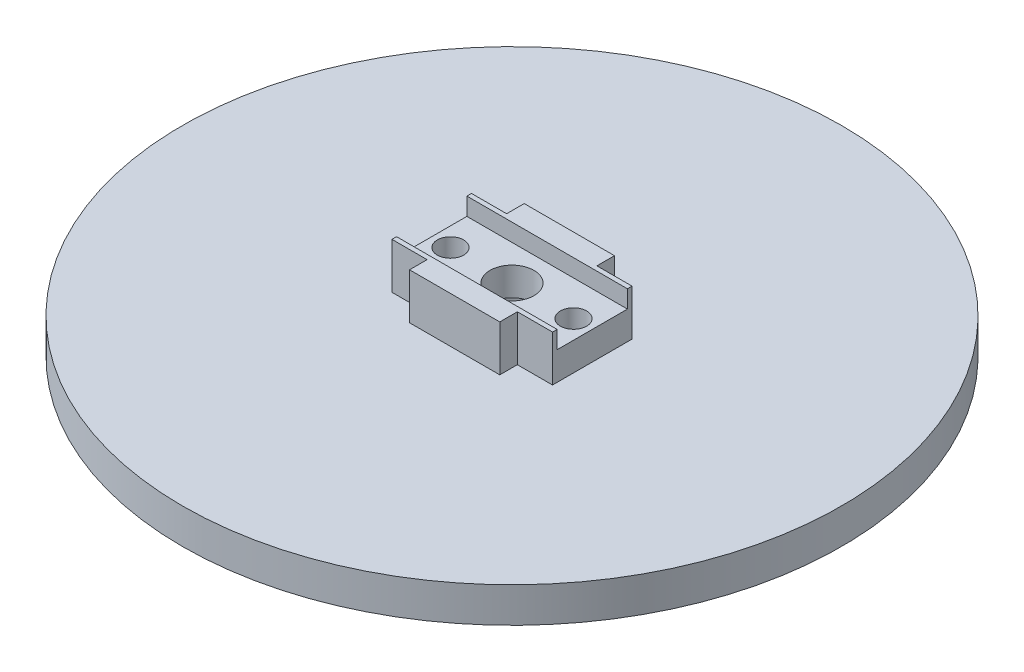
SolidWorks part; units mm, degrees
ref_plane "Front Plane" through (0, 0, 0) normal (0, 0, 1) x (1, 0, 0)
ref_plane "Top Plane" through (0, 0, 0) normal (0, 1, 0) x (1, 0, 0)
ref_plane "Right Plane" through (0, 0, 0) normal (1, 0, 0) x (0, 0, -1)
sketch "Sketch1" plane through (0, 0, 0) normal (0, 1, 0) x (1, 0, 0)
  circle A0 centre (0, 0) radius 37.5
  dimension "D1" = 75
extrude "Boss-Extrude1" add sketch "Sketch1" along normal blind 4
sketch "Sketch2" plane through (0, 4, 0) normal (0, 1, 0) x (1, 0, 0)
  circle A0 centre (0, 0) radius 5.22
  dimension "D1" = 10.44
extrude "Cut-Extrude1" cut sketch "Sketch2" against normal blind 13.05
sketch "Sketch3" plane through (0, 4, 0) normal (0, 1, 0) x (1, 0, 0)
  line L1 (-9.135, 6.525) -> (9.135, 6.525)
  line L2 (-9.135, 6.525) -> (-9.135, -6.525)
  line L3 (-9.135, -6.525) -> (9.135, -6.525)
  line L4 (9.135, 6.525) -> (9.135, -6.525)
  point P4 (0, 0)
  point P5 (0, 0)
  dimension "D1" = 9.135
  dimension "D2" = 9.135
  dimension "D3" = 6.525
  dimension "D4" = 6.525
extrude "Boss-Extrude2" add sketch "Sketch3" along normal blind 5.22
sketch "Sketch4" plane through (0, 9.22, 0) normal (0, 1, 0) x (1, 0, 0)
  line L0 (-9.135, -4.525) -> (-9.135, -6.525)
  line L1 (-9.135, 6.525) -> (-5.135, 6.525)
  line L2 (-9.135, 6.525) -> (-9.135, 4.525)
  line L3 (-9.135, -6.525) -> (-5.135, -6.525)
  line L4 (9.135, 6.525) -> (9.135, 4.525)
  line L6 (-5.135, 6.525) -> (-5.135, 4.525)
  line L8 (5.135, 6.525) -> (5.135, 4.525)
  line L9 (9.135, 4.525) -> (5.135, 4.525)
  line L11 (9.135, -4.525) -> (5.135, -4.525)
  line L13 (-5.135, -4.525) -> (-5.135, -6.525)
  line L14 (-5.135, -4.525) -> (-9.135, -4.525)
  line L15 (5.135, -6.525) -> (9.135, -6.525)
  line L16 (-5.135, 4.525) -> (-9.135, 4.525)
  line L17 (5.135, 6.525) -> (9.135, 6.525)
  line L18 (5.135, -4.525) -> (5.135, -6.525)
  line L19 (9.135, -4.525) -> (9.135, -6.525)
  dimension "D1" = 2
  dimension "D2" = 2
  dimension "D3" = 4
  dimension "D4" = 4
extrude "Cut-Extrude2" cut sketch "Sketch4" against normal up to surface (5.22 mm away) up to face at (0, 4, 37.5)
sketch "Sketch5" plane through (0, 9.22, 0) normal (0, 1, 0) x (1, 0, 0)
  line L1 (-26.8323, 4) -> (26.8323, 4)
  line L2 (-26.8323, 4) -> (-26.8323, -4)
  line L3 (-26.8323, -4) -> (26.8323, -4)
  line L4 (26.8323, 4) -> (26.8323, -4)
  line L5 (-26.8323, 4) -> (26.8323, -4) construction
  line L6 (-26.8323, -4) -> (26.8323, 4) construction
  point P0 (0, 0)
  dimension "D1" = 8
extrude "Cut-Extrude3" cut sketch "Sketch5" against normal blind 2
sketch "Sketch6" plane through (0, 7.22, 0) normal (0, 1, 0) x (1, 0, 0)
  line L0 (5.135, 6.525) -> (-5.135, 6.525) construction
  circle A0 centre (-7, 0) radius 1.5
  circle A1 centre (7, 0) radius 1.5
  point P8 (0, 0)
  dimension "D1" = 3
  dimension "D2" = 3
  dimension "D3" = 6.525
  dimension "D4" = 7
  dimension "D5" = 7
extrude "Cut-Extrude4" cut sketch "Sketch6" against normal blind 4
sketch "Sketch7" plane through (0, 7.22, 0) normal (0, 1, 0) x (1, 0, 0)
  circle A0 centre (0, 0) radius 2.5
  dimension "D1" = 5
extrude "Cut-Extrude5" cut sketch "Sketch7" against normal through all
